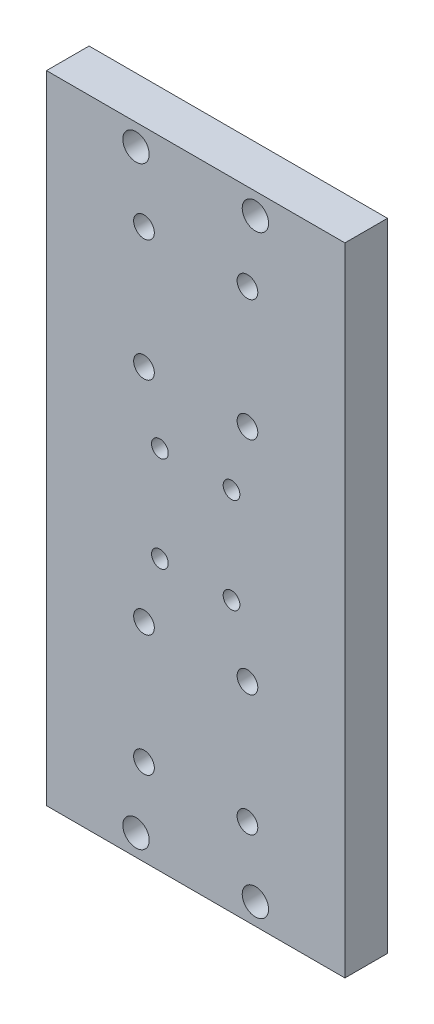
SolidWorks part; units mm, degrees
ref_plane "Plano frontal" through (0, 0, 0) normal (0, 0, 1) x (1, 0, 0)
ref_plane "Plano superior" through (0, 0, 0) normal (0, 1, 0) x (1, 0, 0)
ref_plane "Plano direito" through (0, 0, 0) normal (1, 0, 0) x (0, 0, -1)
sketch "Esboço1" plane through (0, 0, 0) normal (0, 0, 1) x (1, 0, 0)
  line L1 (37.5, 80) -> (-37.5, 80)
  line L2 (37.5, 80) -> (37.5, -80)
  line L3 (37.5, -80) -> (-37.5, -80)
  line L4 (-37.5, 80) -> (-37.5, -80)
  line L5 (37.5, 80) -> (-37.5, -80) construction
  line L6 (37.5, -80) -> (-37.5, 80) construction
  point P0 (0, 0)
  dimension "D1" = 75
  dimension "D2" = 160
extrude "Ressalto-extrusão1" add sketch "Esboço1" along normal blind 10.7
hole_wizard "Furo roscado para conduíte de 1/4-281" positions "Esboço2" profile "Esboço3" tap size "1/4-28" standard "Helicoil® Inch"
sketch "Esboço2" plane through (0, 0, 0) normal (0, 0, -1) x (-1, 0, 0)
  line L0 (37.5, 80) -> (37.5, -80) construction
  line L1 (-37.5, 80) -> (37.5, 80) construction
  line L2 (0, 0) -> (0, 34.0463) construction
  line L4 (0, 0) -> (26.2281, 0) construction
  point P7 (15, 74.65)
  point P25 (-15, 74.65)
  point P27 (15, -74.65)
  point P28 (-15, -74.65)
  dimension "D1" = 22.5
  dimension "D2" = 5.35
sketch "Esboço3" plane through (-15, 74.65, 0) normal (1, 0, 0) x (0, 1, 0)
  line L0 (0, 0) -> (0, 16.9917)
  line L1 (0, 16.9917) -> (3.3147, 15)
  line L2 (3.3147, 15) -> (3.3147, 0)
  line L5 (3.3147, 0) -> (0, 0)
  line L10 (0, 16.9917) -> (-3.3147, 15) construction
  line L11 (0, -6.35) -> (0, 107.95) construction
  dimension "Tap Drill Dia." = 6.6294
  dimension "Tap Drill Depth" = 15
  dimension "Drill Angle" = 118
cosmetic thread "Rosca de furo1" parameters "D1"=15, "D2"=7.6073
cosmetic thread "Rosca de furo2" parameters "D1"=15, "D2"=7.6073
cosmetic thread "Rosca de furo3" parameters "D1"=15, "D2"=7.6073
cosmetic thread "Rosca de furo4" parameters "D1"=15, "D2"=7.6073
hole_wizard "Furo roscado para conduíte de M5x0.81" positions "Esboço4" profile "Esboço5" tap size "M5x0.8" standard "Helicoil® Metric"
sketch "Esboço4" plane through (0, 0, 0) normal (0, 0, -1) x (-1, 0, 0)
  line L0 (37.5, 80) -> (37.5, -80) construction
  line L1 (0, 0) -> (0, 27.75) construction
  line L3 (0, 0) -> (32.3433, 0) construction
  circle A0 centre (15, 74.65) radius 3.3147 construction
  point P0 (13, 58.25)
  point P2 (13, 27.75)
  point P20 (-13, 27.75)
  point P21 (-13, 58.25)
  point P23 (13, -27.75)
  point P24 (-13, -27.75)
  point P25 (13, -58.25)
  point P26 (-13, -58.25)
  dimension "D1" = 16.4
  dimension "D2" = 30.5
  dimension "D3" = 24.5
sketch "Esboço5" plane through (-13, 58.25, 0) normal (1, 0, 0) x (0, 1, 0)
  line L0 (0, 0) -> (0, 16.5622)
  line L1 (0, 16.5622) -> (2.6, 15)
  line L2 (2.6, 15) -> (2.6, 0)
  line L5 (2.6, 0) -> (0, 0)
  line L10 (0, 16.5622) -> (-2.6, 15) construction
  line L11 (0, -6.35) -> (0, 107.95) construction
  dimension "Tap Drill Dia." = 5.2
  dimension "Tap Drill Depth" = 15
  dimension "Drill Angle" = 118
cosmetic thread "Rosca de furo5" parameters "D1"=15, "D2"=6.145
cosmetic thread "Rosca de furo6" parameters "D1"=15, "D2"=6.145
cosmetic thread "Rosca de furo7" parameters "D1"=15, "D2"=6.145
cosmetic thread "Rosca de furo8" parameters "D1"=15, "D2"=6.145
cosmetic thread "Rosca de furo9" parameters "D1"=15, "D2"=6.145
cosmetic thread "Rosca de furo10" parameters "D1"=15, "D2"=6.145
cosmetic thread "Rosca de furo11" parameters "D1"=15, "D2"=6.145
cosmetic thread "Rosca de furo12" parameters "D1"=15, "D2"=6.145
hole_wizard "Furo roscado para conduíte de M4x0.71" positions "Esboço6" profile "Esboço7" tap size "M4x0.7" standard "Helicoil® Metric"
sketch "Esboço6" plane through (0, 0, 0) normal (0, 0, -1) x (-1, 0, 0)
  line L0 (0, 0) -> (29.6452, 0) construction
  line L2 (0, 0) -> (0, 38.9171) construction
  line L4 (37.5, 80) -> (37.5, -80) construction
  circle A0 centre (13, 27.75) radius 2.6 construction
  point P0 (9, 12)
  point P18 (-9, 12)
  point P20 (9, -12)
  point P21 (-9, -12)
  dimension "D1" = 15.75
  dimension "D2" = 28.5
sketch "Esboço7" plane through (-9, 12, 0) normal (1, 0, 0) x (0, 1, 0)
  line L0 (0, 0) -> (0, 16.2618)
  line L1 (0, 16.2618) -> (2.1, 15)
  line L2 (2.1, 15) -> (2.1, 0)
  line L5 (2.1, 0) -> (0, 0)
  line L10 (0, 16.2618) -> (-2.1, 15) construction
  line L11 (0, -6.35) -> (0, 107.95) construction
  dimension "Tap Drill Dia." = 4.2
  dimension "Tap Drill Depth" = 15
  dimension "Drill Angle" = 118
cosmetic thread "Rosca de furo13" parameters "D1"=15, "D2"=5.007
cosmetic thread "Rosca de furo14" parameters "D1"=15, "D2"=5.007
cosmetic thread "Rosca de furo15" parameters "D1"=15, "D2"=5.007
cosmetic thread "Rosca de furo16" parameters "D1"=15, "D2"=5.007
sketch "Esboço8" plane through (0, 0, 0) normal (0, 0, -1) x (-1, 0, 0)
  line L0 (-54.4525, 0) -> (58.7956, 0) construction
  line L1 (0, 0) -> (0, 65.9234) construction
  circle A0 centre (-13, 58.25) radius 4.25
  circle A2 centre (-13, 27.75) radius 4.25
  circle A4 centre (13, 27.75) radius 4.25
  circle A5 centre (13, 58.25) radius 4.25
  circle A6 centre (13, -27.75) radius 4.25
  circle A7 centre (-13, -27.75) radius 4.25
  circle A8 centre (13, -58.25) radius 4.25
  circle A9 centre (-13, -58.25) radius 4.25
  dimension "D1" = 8.5
extrude "Corte-extrusão1" cut sketch "Esboço8" against normal blind 5
sketch "Esboço9" plane through (0, 0, 0) normal (0, 0, -1) x (-1, 0, 0)
  circle A0 centre (-9, 12) radius 3.5
  circle A1 centre (9, 12) radius 3.5
  circle A2 centre (-9, -12) radius 3.5
  circle A3 centre (9, -12) radius 3.5
  dimension "D1" = 7
extrude "Corte-extrusão2" cut sketch "Esboço9" against normal blind 4
